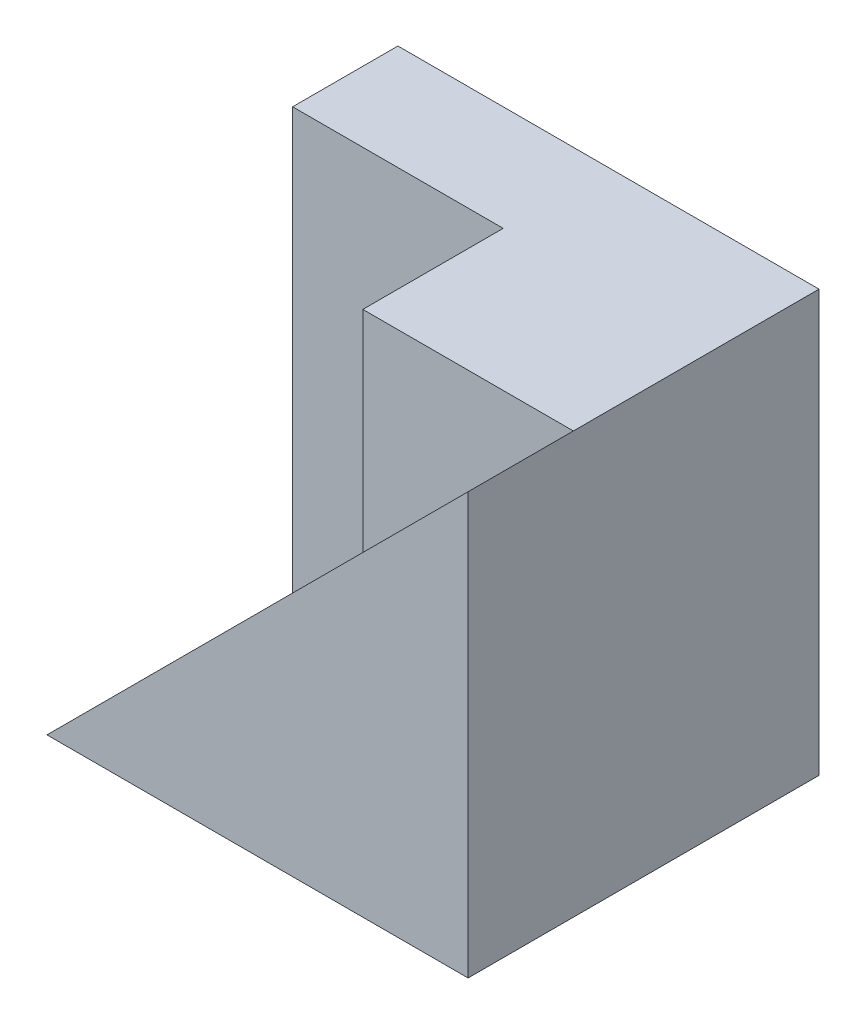
SolidWorks part; units mm, degrees
ref_plane "Front Plane" through (0, 0, 0) normal (0, 0, 1) x (1, 0, 0)
ref_plane "Top Plane" through (0, 0, 0) normal (0, 1, 0) x (1, 0, 0)
ref_plane "Right Plane" through (0, 0, 0) normal (1, 0, 0) x (0, 0, -1)
sketch "Sketch1" plane through (0, 0, 0) normal (0, 1, 0) x (1, 0, 0)
  line L1 (-3, -2.5) -> (3, -2.5)
  line L2 (-3, -2.5) -> (-3, 2.5)
  line L3 (-3, 2.5) -> (3, 2.5)
  line L4 (3, -2.5) -> (3, 2.5)
  line L5 (-3, -2.5) -> (3, 2.5) construction
  line L6 (-3, 2.5) -> (3, -2.5) construction
  point P0 (0, 0)
  dimension "D1" = 5
  dimension "D2" = 6
extrude "Boss-Extrude1" add sketch "Sketch1" along normal blind 6
sketch "Sketch2" plane through (0, 0, 2.5) normal (0, 0, 1) x (1, 0, 0)
  line L0 (3, 6) -> (-3, 0)
  line L1 (-3, 0) -> (-3, 6)
  line L2 (-3, 6) -> (3, 6)
extrude "Cut-Extrude1" cut sketch "Sketch2" against normal blind 3.5
sketch "Sketch3" plane through (0, 6, 0) normal (0, 1, 0) x (1, 0, 0)
  line L0 (3, 1) -> (-3, 1) construction
  line L1 (0, 1) -> (3, 1)
  line L2 (0, 1) -> (0, -1)
  line L3 (0, -1) -> (3, -1)
  line L4 (3, 1) -> (3, -1)
  line L5 (3, -2.5) -> (3, 1) construction
  dimension "D1" = 2
  dimension "D2" = 3
extrude "Boss-Extrude2" add sketch "Sketch3" against normal blind 3
